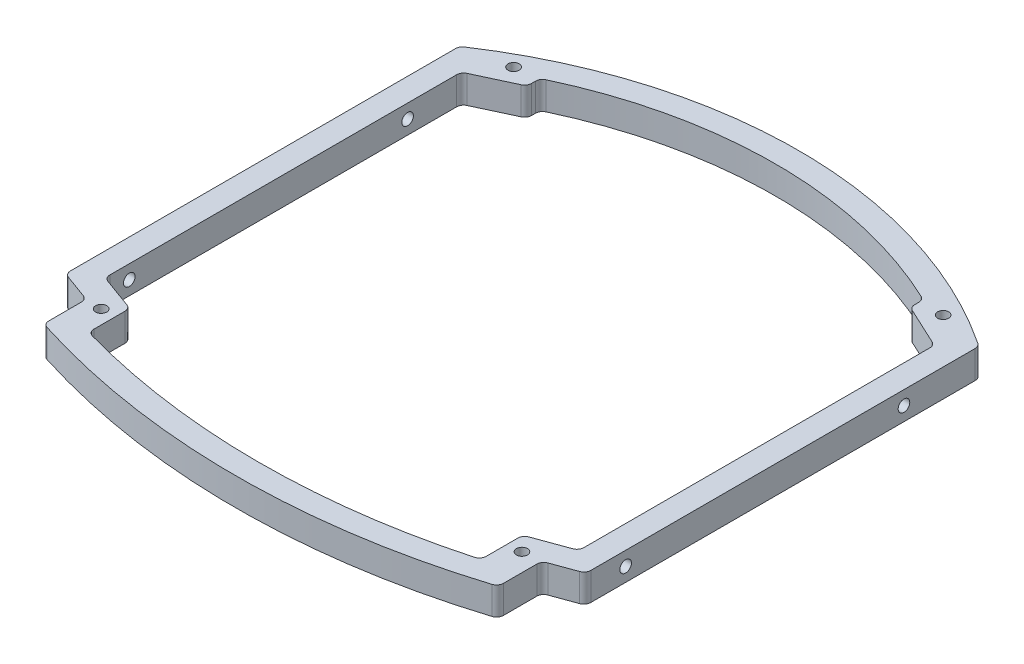
SolidWorks part; units mm, degrees
ref_plane "Front Plane" through (0, 0, 0) normal (0, 0, 1) x (1, 0, 0)
ref_plane "Top Plane" through (0, 0, 0) normal (0, 1, 0) x (1, 0, 0)
ref_plane "Right Plane" through (0, 0, 0) normal (1, 0, 0) x (0, 0, -1)
sketch "Sketch1" plane through (0, 0, 0) normal (0, 1, 0) x (1, 0, 0)
  line L0 (-56, -46.8789) -> (-56, 38)
  line L1 (56, -46.6969) -> (56, 38)
  line L2 (-51, -43.3778) -> (-51, 33.3948)
  line L3 (51, 33.3948) -> (51, -43.1959)
  line L4 (-56, -46.8789) -> (-49, -49.4267)
  line L5 (-49, -49.4267) -> (-49, -58.5744)
  line L6 (49, -58.5744) -> (49, -49.2447)
  line L7 (49, -49.2447) -> (56, -46.6969)
  line L10 (-51, -43.3778) -> (-42.6, -46.4352)
  line L11 (-50, 45) -> (50, 45) construction
  line L12 (-50, 45) -> (-50, -55) construction
  line L13 (-50, -55) -> (50, -55) construction
  line L14 (50, 45) -> (50, -55) construction
  line L15 (-42.6, -46.4352) -> (-42.6, -55.2932)
  line L16 (42.1, -55.4352) -> (42.1, -46.4352)
  line L17 (42.1, -46.4352) -> (51, -43.1959)
  line L18 (41.3, 40.7037) -> (41.3, 37.918)
  line L19 (41.3, 37.918) -> (51, 33.3948)
  line L20 (-51, 33.3948) -> (-41.3, 37.918)
  line L21 (-41.3, 37.918) -> (-41.3, 40.7037)
  arc A0 (-56, 38) -> (56, 38) centre (0, -44.8493) cw
  arc A1 (-49, -58.5744) -> (49, -58.5744) centre (0, 93.7378) ccw
  arc A2 (-41.3, 40.7037) -> (41.3, 40.7037) centre (0, -44.8493) cw
  arc A3 (42.1, -55.4352) -> (-42.6, -55.2932) centre (0, 93.7378) cw
  circle A4 centre (-46.3, 40) radius 1.2
  circle A5 centre (46.3, 40) radius 1.2
  circle A6 centre (45.1, -49.6) radius 1.2
  circle A7 centre (-45.6, -49.6) radius 1.2
  dimension "D11" = 100
  dimension "D7" = 160
  dimension "D9" = 2.4
  dimension "D19" = 5
  dimension "D36" = 5
  dimension "D5" = 7
  dimension "D3" = 56
  dimension "D6" = 100
  dimension "D4" = 5
  dimension "D8" = 50
  dimension "D10" = 4.4
  dimension "D12" = 5.4
  dimension "D13" = 3.7
  dimension "D14" = 5
  dimension "D15" = 3.7
  dimension "D16" = 5
  dimension "D17" = 5.4
  dimension "D18" = 4.9
  dimension "D20" = 4
  dimension "D21" = 3
  dimension "D22" = 110
  dimension "D23" = 3
  dimension "D24" = 4
  dimension "D25" = 110
  dimension "D26" = 4
  dimension "D27" = 5
  dimension "D28" = 115
  dimension "D29" = 5
  dimension "D30" = 4
  dimension "D31" = 115
  dimension "D32" = 40
  dimension "D33" = 5
  dimension "D34" = 2
  dimension "D35" = 7
  dimension "D37" = 5
  dimension "D38" = 5
  dimension "D39" = 9
  dimension "D40" = 112
extrude "Boss-Extrude1" add sketch "Sketch1" along normal blind 6
hole_wizard "Tap Drill for M3 Tap1" positions "Sketch3" profile "Sketch2" hole size "M3" standard "ISO"
sketch "Sketch3" plane through (-56, 0, 0) normal (-1, 0, 0) x (0, 0, 1)
  line L0 (-38, 0) -> (46.8789, 0) construction
  line L1 (56.1421, 6) -> (56.1421, 0) construction
  point P0 (-21.8579, 3)
  point P2 (38.1421, 3)
  dimension "D1" = 3
  dimension "D2" = 3
  dimension "D3" = 60
  dimension "D4" = 18
sketch "Sketch2" plane through (-56, 3, -21.8579) normal (0, 1, 0) x (0, 0, 1)
  line L0 (0, 0) -> (0, 10.7511)
  line L1 (0, 10.7511) -> (1.25, 10)
  line L2 (1.25, 10) -> (1.25, 0)
  line L5 (1.25, 0) -> (0, 0)
  line L10 (0, 10.7511) -> (-1.25, 10) construction
  line L11 (0, -6.35) -> (0, 107.95) construction
  dimension "Hole Dia." = 2.5
  dimension "Hole Depth" = 10
  dimension "Drill Angle" = 118
mirror "Mirror1" about plane through (0, 0, 0) normal (1, 0, 0) of "Tap Drill for M3 Tap1"
fillet "Fillet1" radius 1.5 20 edges at (56, 3, -38) (-56, 3, -38) (-56, 3, 46.8789) (49, 3, 49.2447) (56, 3, 46.6969) (49, 3, 58.5744) (-49, 3, 58.5744) (-49, 3, 49.4267) (-42.6, 3, 55.2932) (-42.6, 3, 46.4352) (-51, 3, 43.3778) (42.1, 3, 55.4352) (42.1, 3, 46.4352) (51, 3, 43.1959) (51, 3, -33.3948) (41.3, 3, -37.918) (41.3, 3, -40.7037) (-51, 3, -33.3948) (-41.3, 3, -40.7037) (-41.3, 3, -37.918)
